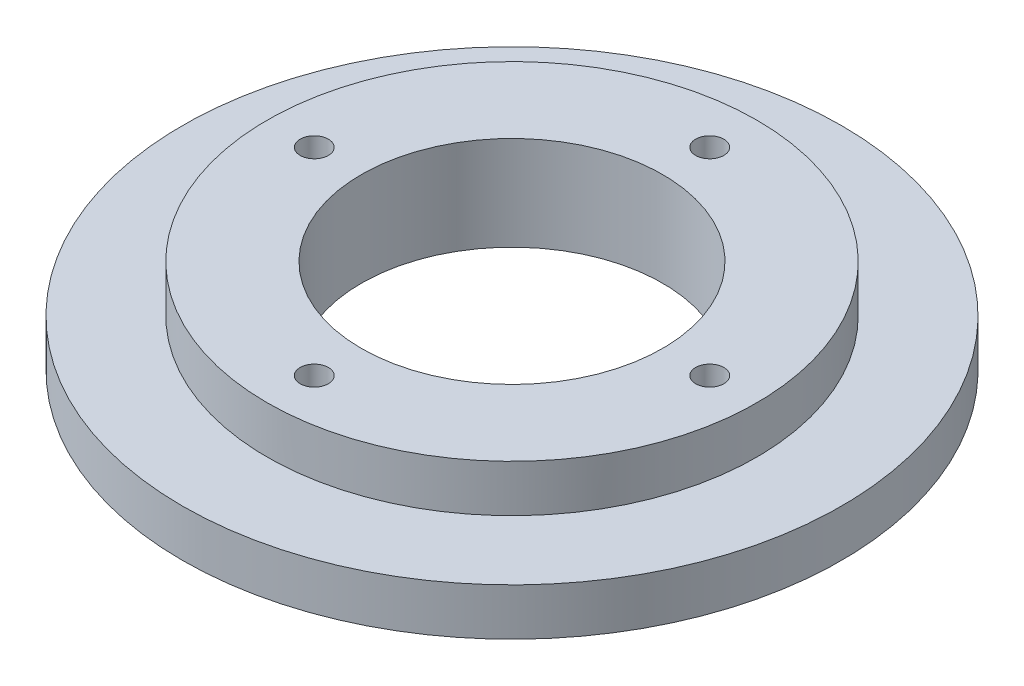
SolidWorks part; units mm, degrees
ref_plane "Front Plane" through (0, 0, 0) normal (0, 0, 1) x (1, 0, 0)
ref_plane "Top Plane" through (0, 0, 0) normal (0, 1, 0) x (1, 0, 0)
ref_plane "Right Plane" through (0, 0, 0) normal (1, 0, 0) x (0, 0, -1)
sketch "Esquisse1" plane through (0, 0, 0) normal (0, 1, 0) x (1, 0, 0)
  circle A0 centre (0, 0) radius 26
  circle A2 centre (0, 0) radius 16
  dimension "D1" = 52
  dimension "D2" = 10
extrude "Boss.-Extru.1" add sketch "Esquisse1" along normal blind 10
sketch "Esquisse2" plane through (0, 0, 0) normal (0, -1, 0) x (1, 0, 0)
  circle A0 centre (0, 0) radius 35
  circle A1 centre (0, 0) radius 16
  dimension "D1" = 70
extrude "Boss.-Extru.2" add sketch "Esquisse2" against normal blind 5 contours A0
sketch "Esquisse3" plane through (0, 5, 0) normal (0, 1, 0) x (1, 0, 0)
  circle A0 centre (0, 0) radius 16
extrude "Enlèv. mat.-Extru.1" cut sketch "Esquisse3" against normal blind 5
sketch "Esquisse4" plane through (0, 10, 0) normal (0, 1, 0) x (1, 0, 0)
  circle A0 centre (0, 0) radius 21
  circle A1 centre (0, 0) radius 26 construction
  circle A2 centre (-21, 0) radius 1.5
  circle A4 centre (21, 0) radius 1.5
  circle A5 centre (0, -21) radius 1.5
  circle A8 centre (0, 21) radius 1.5
  circle M2 centre (0, 0) radius 16
  dimension "D1" = 5
  dimension "D2" = 3
  dimension "D3" = 3
  dimension "D4" = 3
  dimension "D5" = 3
extrude "Enlèv. mat.-Extru.2" cut sketch "Esquisse4" against normal blind 35 contours A0 A5 | A0 A5 | A8 M2 | A8 M2 | A2 | A4
sketch "Esquisse5" plane through (0, 0, 0) normal (0, -1, 0) x (1, 0, 0)
  line L1 (24.0311, 0) -> (22.5155, 2.625)
  line L2 (22.5155, 2.625) -> (19.4845, 2.625)
  line L3 (19.4845, 2.625) -> (17.9689, 0)
  line L4 (17.9689, 0) -> (19.4845, -2.625)
  line L5 (19.4845, -2.625) -> (22.5155, -2.625)
  line L6 (22.5155, -2.625) -> (24.0311, 0)
  line L7 (3.0311, -21) -> (1.5155, -18.375)
  line L8 (1.5155, -18.375) -> (-1.5155, -18.375)
  line L9 (-1.5155, -18.375) -> (-3.0311, -21)
  line L10 (-3.0311, -21) -> (-1.5155, -23.625)
  line L11 (-1.5155, -23.625) -> (1.5155, -23.625)
  line L12 (1.5155, -23.625) -> (3.0311, -21)
  line L13 (-17.9689, 0) -> (-19.4845, 2.625)
  line L14 (-19.4845, 2.625) -> (-22.5155, 2.625)
  line L15 (-22.5155, 2.625) -> (-24.0311, 0)
  line L16 (-24.0311, 0) -> (-22.5155, -2.625)
  line L17 (-22.5155, -2.625) -> (-19.4845, -2.625)
  line L18 (-19.4845, -2.625) -> (-17.9689, 0)
  line L19 (3.0311, 21) -> (1.5155, 23.625)
  line L20 (1.5155, 23.625) -> (-1.5155, 23.625)
  line L21 (-1.5155, 23.625) -> (-3.0311, 21)
  line L22 (-3.0311, 21) -> (-1.5155, 18.375)
  line L23 (-1.5155, 18.375) -> (1.5155, 18.375)
  line L24 (1.5155, 18.375) -> (3.0311, 21)
  circle A0 centre (21, 0) radius 2.625 construction
  circle A1 centre (0, -21) radius 2.625 construction
  circle A2 centre (-21, 0) radius 2.625 construction
  circle A3 centre (0, 21) radius 2.625 construction
  point P28 (0, 23.625)
  dimension "D1" = 5.25
  dimension "D2" = 5.25
  dimension "D3" = 5.25
  dimension "D4" = 5.25
extrude "Enlèv. mat.-Extru.3" cut sketch "Esquisse5" against normal blind 3
